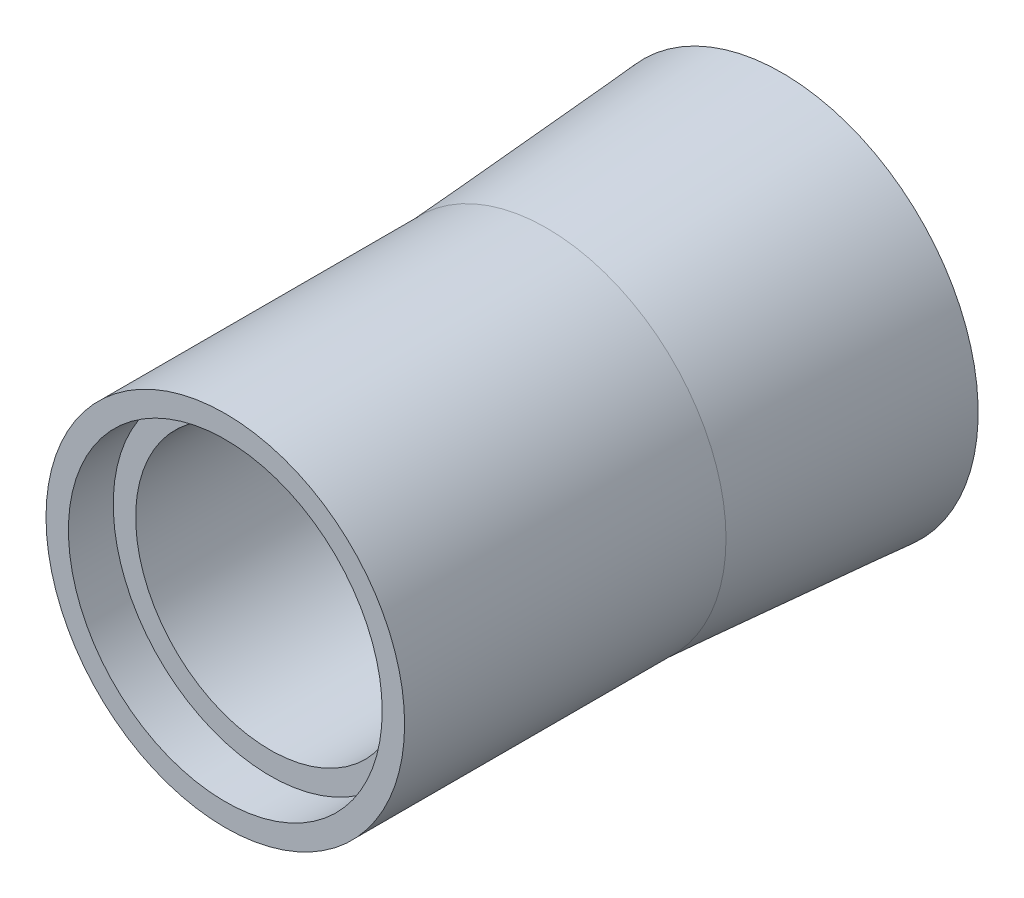
SolidWorks part; units mm, degrees
material "Epoxy, Unfilled"
ref_plane "Front Plane" through (0, 0, 0) normal (0, 0, 1) x (1, 0, 0)
ref_plane "Top Plane" through (0, 0, 0) normal (0, 1, 0) x (1, 0, 0)
ref_plane "Right Plane" through (0, 0, 0) normal (1, 0, 0) x (0, 0, -1)
sketch "Sketch1" plane through (0, 0, 0) normal (0, 0, 1) x (1, 0, 0)
  circle A0 centre (0, 0) radius 38.1
  circle A1 centre (0, 0) radius 50.8
  dimension "D1" = 76.2
  dimension "D2" = 12.7
extrude "Boss-Extrude1" add sketch "Sketch1" along normal blind 157.734
sketch "Sketch2" plane through (0, 0, 157.734) normal (0, 0, 1) x (1, 0, 0)
  circle A0 centre (0, 0) radius 50.8
  circle A1 centre (0, 0) radius 44.45
  circle A2 centre (0, 0) radius 50.8 construction
  circle M4 centre (0, 0) radius 38.1
  dimension "D1" = 6.35
extrude "Cut-Extrude1" cut sketch "Sketch2" against normal blind 12.7 contours M4 | A1 M4
sketch "Sketch3" plane through (0, 0, 0) normal (0, 1, 0) x (1, 0, 0)
  line L0 (0, 0) -> (55.5625, 0) construction
  line L1 (38.1, 0) -> (-38.1, 0) construction
  line L2 (55.5625, 0) -> (50.8, -66.675)
  line L3 (50.8, -66.675) -> (50.8, 0)
  line L4 (55.5625, 0) -> (50.8, 0)
  line L5 (0, 0) -> (0, -110.1696) construction
  dimension "D1" = 66.675
  dimension "D2" = 55.5625
  dimension "D3" = 50.8
revolve "Revolve1" add sketch "Sketch3" angle 360 about L5
